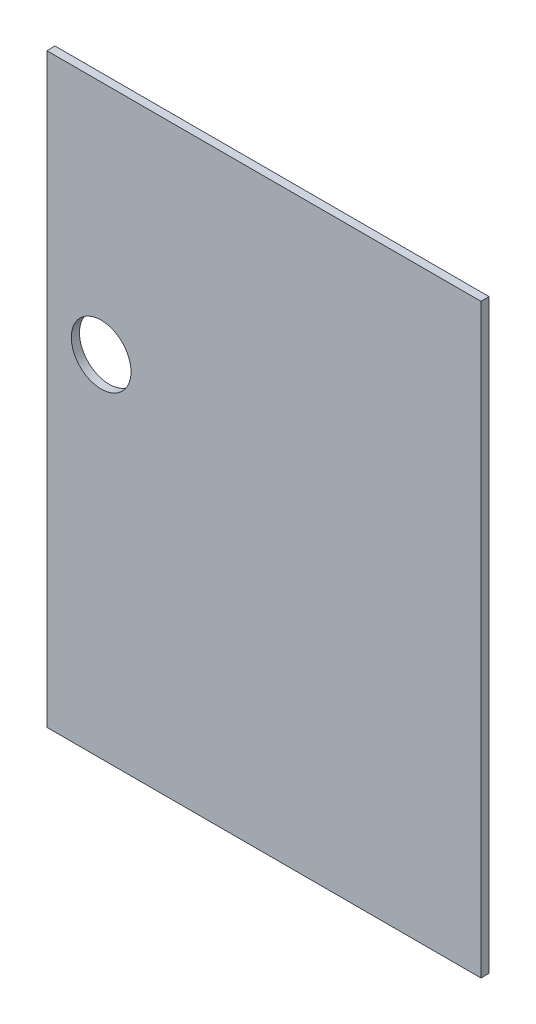
SolidWorks part; units mm, degrees
ref_plane "Front Plane" through (0, 0, 0) normal (0, 0, 1) x (1, 0, 0)
ref_plane "Top Plane" through (0, 0, 0) normal (0, 1, 0) x (1, 0, 0)
ref_plane "Right Plane" through (0, 0, 0) normal (1, 0, 0) x (0, 0, -1)
sketch "Sketch1" plane through (0, 0, 0) normal (0, 0, 1) x (1, 0, 0)
  line L1 (0, 0) -> (160, 0)
  line L2 (0, 0) -> (0, 216)
  line L3 (0, 216) -> (160, 216)
  line L4 (160, 0) -> (160, 216)
  dimension "D1" = 160
  dimension "D2" = 216
extrude "Boss-Extrude1" add sketch "Sketch1" along normal blind 3
sketch "Sketch2" plane through (0, 0, 3) normal (0, 0, 1) x (1, 0, 0)
  line L1 (0, 0) -> (160, 0) construction
  line L2 (0, 216) -> (0, 0) construction
  circle A0 centre (20, 129) radius 11
  point P2 (0, 0)
  dimension "D1" = 22
  dimension "D2" = 20
  dimension "D3" = 129
extrude "Cut-Extrude1" cut sketch "Sketch2" against normal blind 3
